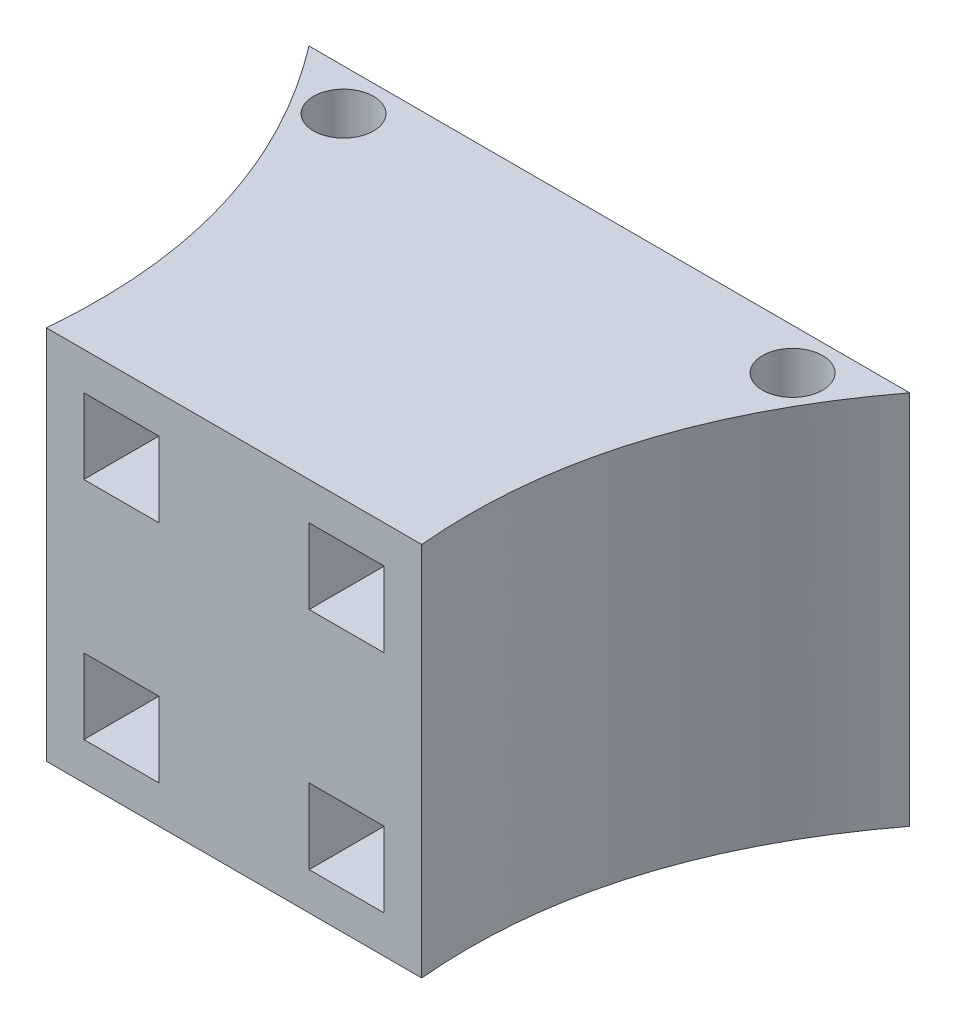
SolidWorks part; units mm, degrees
ref_plane "Front Plane" through (0, 0, 0) normal (0, 0, 1) x (1, 0, 0)
ref_plane "Top Plane" through (0, 0, 0) normal (0, 1, 0) x (1, 0, 0)
ref_plane "Right Plane" through (0, 0, 0) normal (1, 0, 0) x (0, 0, -1)
sketch "Sketch2" plane through (0, 0, 0) normal (0, 1, 0) x (1, 0, 0)
  line L0 (0, 0) -> (127, 0)
  line L1 (63.5, 0) -> (63.5, 126.9649) construction
  line L2 (165.1, 126.9649) -> (-38.1, 126.9649)
  spline S0 degree 2 poles (0, 0) (6.3597, 68.4699) (-38.1, 126.9649) knots 0 0 0 1 1 1
  spline S1 degree 2 poles (127, 0) (120.6403, 68.4699) (165.1, 126.9649) knots 0 0 0 1 1 1
  point P8 (63.5, 126.9649)
  dimension "D3" = 135.829
  dimension "D5" = 135.829
  dimension "D1" = 127
  dimension "D2" = 203.2
  dimension "D4" = 33.6494
extrude "Boss-Extrude1" add sketch "Sketch2" against normal blind 127
sketch "Sketch3" plane through (0, 0, 0) normal (0, 0, 1) x (1, 0, 0)
  line L0 (0, 0) -> (127, 0) construction
  line L1 (12.7, -12.7) -> (38.1, -12.7)
  line L2 (12.7, -12.7) -> (12.7, -38.1)
  line L3 (12.7, -38.1) -> (38.1, -38.1)
  line L4 (38.1, -12.7) -> (38.1, -38.1)
  line L5 (38.1, -88.9) -> (12.7, -88.9)
  line L6 (38.1, -88.9) -> (38.1, -114.3)
  line L7 (38.1, -114.3) -> (12.7, -114.3)
  line L8 (12.7, -88.9) -> (12.7, -114.3)
  line L9 (88.9, -12.7) -> (114.3, -12.7)
  line L10 (88.9, -12.7) -> (88.9, -38.1)
  line L11 (88.9, -38.1) -> (114.3, -38.1)
  line L12 (114.3, -12.7) -> (114.3, -38.1)
  line L13 (88.9, -88.9) -> (114.3, -88.9)
  line L14 (88.9, -88.9) -> (88.9, -114.3)
  line L15 (88.9, -114.3) -> (114.3, -114.3)
  line L16 (114.3, -88.9) -> (114.3, -114.3)
  line L17 (0, -127) -> (0, 0) construction
  line L18 (0, -127) -> (127, -127) construction
  line L19 (127, -127) -> (127, 0) construction
  dimension "D1" = 12.7
  dimension "D2" = 12.7
  dimension "D3" = 12.7
  dimension "D4" = 12.7
  dimension "D5" = 12.7
  dimension "D6" = 12.7
  dimension "D7" = 12.7
  dimension "D8" = 12.7
  dimension "D9" = 25.4
  dimension "D10" = 25.4
  dimension "D11" = 25.4
  dimension "D12" = 25.4
  dimension "D13" = 25.4
  dimension "D14" = 25.4
  dimension "D15" = 25.4
  dimension "D16" = 25.4
extrude "Cut-Extrude1" cut sketch "Sketch3" against normal blind 63.5
sketch "Sketch4" plane through (0, 0, 0) normal (0, 1, 0) x (1, 0, 0)
  line L0 (165.1, 126.9649) -> (-38.1, 126.9649) construction
  circle A0 centre (-12.4473, 112.9949) radius 10.16
  circle A1 centre (139.4473, 112.9949) radius 10.16
  dimension "D1" = 20.32
  dimension "D2" = 20.32
  dimension "D4" = 13.97
  dimension "D6" = 13.97
  dimension "D3" = 29.21
  dimension "D5" = 29.21
extrude "Cut-Extrude2" cut sketch "Sketch4" against normal through all
